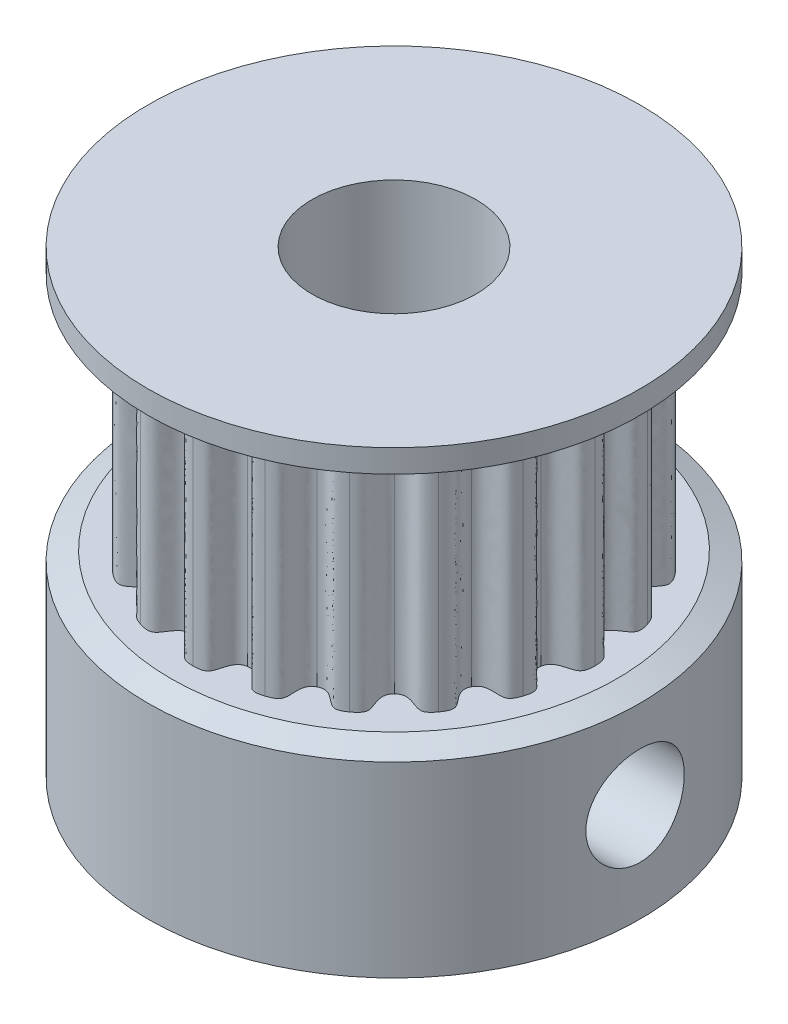
SolidWorks part; units mm, degrees
material "6063-T5"
ref_plane "Front Plane" through (0, 0, 0) normal (0, 0, 1) x (1, 0, 0)
ref_plane "Top Plane" through (0, 0, 0) normal (0, 1, 0) x (1, 0, 0)
ref_plane "Right Plane" through (0, 0, 0) normal (1, 0, 0) x (0, 0, -1)
sketch "Sketch1" plane through (0, 0, 0) normal (0, 1, 0) x (1, 0, 0)
  circle A0 centre (0, 0) radius 7.5
  dimension "D1" = 15
extrude "Boss-Extrude1" add sketch "Sketch1" along normal blind 6 contours A0
sketch "Sketch2" plane through (0, 6, 0) normal (0, 1, 0) x (1, 0, 0)
  line L0 (0, 6.1275) -> (0, 5.3775) construction
  line L1 (1.8935, 5.8276) -> (1.6617, 5.1143) construction
  line L2 (0.9585, 6.052) -> (0.8412, 5.3113) construction
  circle A0 centre (0, 0) radius 6.1275
  circle A1 centre (0, 0) radius 5.3775 construction
  spline S0 degree 3 poles (0, 6.1275) (0.3458, 6.1275) (0.4361, 5.9343) (0.5475, 5.3578) (0.8412, 5.3113) knots 0 0 0 0 0.372907 1 1 1 1
  spline S1 degree 3 poles (1.8935, 5.8276) (1.5646, 5.9344) (1.419, 5.7786) (1.135, 5.2647) (0.8412, 5.3113) knots 0 0 0 0 0.372907 1 1 1 1
  spline S2 degree 3 poles (3.6016, 4.9572) (3.3681, 5.1259) (3.0728, 5.1167) (2.729, 4.6418) (2.4347, 4.7947) knots 0 0 0 0 0.382401 1 1 1 1
  spline S3 degree 3 poles (1.8935, 5.8276) (2.162, 5.7403) (2.3095, 5.4903) (2.1415, 4.9436) (2.4347, 4.7947) knots 0 0 0 0 0.37474 1 1 1 1
  spline S4 degree 3 poles (4.9572, 3.6016) (4.7873, 3.8342) (4.5035, 3.9167) (4.0298, 3.5713) (3.7972, 3.8077) knots 0 0 0 0 0.382401 1 1 1 1
  spline S5 degree 3 poles (3.6016, 4.9572) (3.83, 4.7913) (3.8931, 4.5079) (3.5643, 4.0399) (3.7972, 3.8077) knots 0 0 0 0 0.37474 1 1 1 1
  spline S6 degree 3 poles (5.8276, 1.8935) (5.7378, 2.1672) (5.4934, 2.3334) (4.9362, 2.1512) (4.788, 2.4479) knots 0 0 0 0 0.382401 1 1 1 1
  spline S7 degree 3 poles (4.9572, 3.6016) (5.1231, 3.3733) (5.0955, 3.0843) (4.6383, 2.7408) (4.788, 2.4479) knots 0 0 0 0 0.37474 1 1 1 1
  spline S8 degree 3 poles (6.1275, 0) (6.1267, 0.288) (5.9456, 0.5216) (5.3594, 0.5206) (5.3101, 0.8485) knots 0 0 0 0 0.382401 1 1 1 1
  spline S9 degree 3 poles (5.8276, 1.8935) (5.9148, 1.625) (5.7992, 1.3587) (5.2582, 1.1733) (5.3101, 0.8485) knots 0 0 0 0 0.37474 1 1 1 1
  spline S10 degree 3 poles (5.8276, -1.8935) (5.9158, -1.6193) (5.8158, -1.3412) (5.2579, -1.1611) (5.3124, -0.8339) knots 0 0 0 0 0.382401 1 1 1 1
  spline S11 degree 3 poles (6.1275, 0) (6.1275, -0.2823) (5.9353, -0.4999) (5.3634, -0.509) (5.3124, -0.8339) knots 0 0 0 0 0.37474 1 1 1 1
  spline S12 degree 3 poles (4.9572, -3.6016) (5.1259, -3.3681) (5.1167, -3.0728) (4.6418, -2.729) (4.7947, -2.4347) knots 0 0 0 0 0.382401 1 1 1 1
  spline S13 degree 3 poles (5.8276, -1.8935) (5.7403, -2.162) (5.4903, -2.3095) (4.9436, -2.1415) (4.7947, -2.4347) knots 0 0 0 0 0.37474 1 1 1 1
  spline S14 degree 3 poles (3.6016, -4.9572) (3.8342, -4.7873) (3.9167, -4.5035) (3.5713, -4.0298) (3.8077, -3.7972) knots 0 0 0 0 0.382401 1 1 1 1
  spline S15 degree 3 poles (4.9572, -3.6016) (4.7913, -3.83) (4.5079, -3.8931) (4.0399, -3.5643) (3.8077, -3.7972) knots 0 0 0 0 0.37474 1 1 1 1
  spline S16 degree 3 poles (1.8935, -5.8276) (2.1672, -5.7378) (2.3334, -5.4934) (2.1512, -4.9362) (2.4479, -4.788) knots 0 0 0 0 0.382401 1 1 1 1
  spline S17 degree 3 poles (3.6016, -4.9572) (3.3733, -5.1231) (3.0843, -5.0955) (2.7408, -4.6383) (2.4479, -4.788) knots 0 0 0 0 0.37474 1 1 1 1
  spline S18 degree 3 poles (0, -6.1275) (0.288, -6.1267) (0.5216, -5.9456) (0.5206, -5.3594) (0.8485, -5.3101) knots 0 0 0 0 0.382401 1 1 1 1
  spline S19 degree 3 poles (1.8935, -5.8276) (1.625, -5.9148) (1.3587, -5.7992) (1.1733, -5.2582) (0.8485, -5.3101) knots 0 0 0 0 0.37474 1 1 1 1
  spline S20 degree 3 poles (-1.8935, -5.8276) (-1.6193, -5.9158) (-1.3412, -5.8158) (-1.1611, -5.2579) (-0.8339, -5.3124) knots 0 0 0 0 0.382401 1 1 1 1
  spline S21 degree 3 poles (0, -6.1275) (-0.2823, -6.1275) (-0.4999, -5.9353) (-0.509, -5.3634) (-0.8339, -5.3124) knots 0 0 0 0 0.37474 1 1 1 1
  spline S22 degree 3 poles (-3.6016, -4.9572) (-3.3681, -5.1259) (-3.0728, -5.1167) (-2.729, -4.6418) (-2.4347, -4.7947) knots 0 0 0 0 0.382401 1 1 1 1
  spline S23 degree 3 poles (-1.8935, -5.8276) (-2.162, -5.7403) (-2.3095, -5.4903) (-2.1415, -4.9436) (-2.4347, -4.7947) knots 0 0 0 0 0.37474 1 1 1 1
  spline S24 degree 3 poles (-4.9572, -3.6016) (-4.7873, -3.8342) (-4.5035, -3.9167) (-4.0298, -3.5713) (-3.7972, -3.8077) knots 0 0 0 0 0.382401 1 1 1 1
  spline S25 degree 3 poles (-3.6016, -4.9572) (-3.83, -4.7913) (-3.8931, -4.5079) (-3.5643, -4.0399) (-3.7972, -3.8077) knots 0 0 0 0 0.37474 1 1 1 1
  spline S26 degree 3 poles (-5.8276, -1.8935) (-5.7378, -2.1672) (-5.4934, -2.3334) (-4.9362, -2.1512) (-4.788, -2.4479) knots 0 0 0 0 0.382401 1 1 1 1
  spline S27 degree 3 poles (-4.9572, -3.6016) (-5.1231, -3.3733) (-5.0955, -3.0843) (-4.6383, -2.7408) (-4.788, -2.4479) knots 0 0 0 0 0.37474 1 1 1 1
  spline S28 degree 3 poles (-6.1275, 0) (-6.1267, -0.288) (-5.9456, -0.5216) (-5.3594, -0.5206) (-5.3101, -0.8485) knots 0 0 0 0 0.382401 1 1 1 1
  spline S29 degree 3 poles (-5.8276, -1.8935) (-5.9148, -1.625) (-5.7992, -1.3587) (-5.2582, -1.1733) (-5.3101, -0.8485) knots 0 0 0 0 0.37474 1 1 1 1
  spline S30 degree 3 poles (-5.8276, 1.8935) (-5.9158, 1.6193) (-5.8158, 1.3412) (-5.2579, 1.1611) (-5.3124, 0.8339) knots 0 0 0 0 0.382401 1 1 1 1
  spline S31 degree 3 poles (-6.1275, 0) (-6.1275, 0.2823) (-5.9353, 0.4999) (-5.3634, 0.509) (-5.3124, 0.8339) knots 0 0 0 0 0.37474 1 1 1 1
  spline S32 degree 3 poles (-4.9572, 3.6016) (-5.1259, 3.3681) (-5.1167, 3.0728) (-4.6418, 2.729) (-4.7947, 2.4347) knots 0 0 0 0 0.382401 1 1 1 1
  spline S33 degree 3 poles (-5.8276, 1.8935) (-5.7403, 2.162) (-5.4903, 2.3095) (-4.9436, 2.1415) (-4.7947, 2.4347) knots 0 0 0 0 0.37474 1 1 1 1
  spline S34 degree 3 poles (-3.6016, 4.9572) (-3.8342, 4.7873) (-3.9167, 4.5035) (-3.5713, 4.0298) (-3.8077, 3.7972) knots 0 0 0 0 0.382401 1 1 1 1
  spline S35 degree 3 poles (-4.9572, 3.6016) (-4.7913, 3.83) (-4.5079, 3.8931) (-4.0399, 3.5643) (-3.8077, 3.7972) knots 0 0 0 0 0.37474 1 1 1 1
  spline S36 degree 3 poles (-1.8935, 5.8276) (-2.1672, 5.7378) (-2.3334, 5.4934) (-2.1512, 4.9362) (-2.4479, 4.788) knots 0 0 0 0 0.382401 1 1 1 1
  spline S37 degree 3 poles (-3.6016, 4.9572) (-3.3733, 5.1231) (-3.0843, 5.0955) (-2.7408, 4.6383) (-2.4479, 4.788) knots 0 0 0 0 0.37474 1 1 1 1
  spline S38 degree 3 poles (0, 6.1275) (-0.288, 6.1267) (-0.5216, 5.9456) (-0.5206, 5.3594) (-0.8485, 5.3101) knots 0 0 0 0 0.382401 1 1 1 1
  spline S39 degree 3 poles (-1.8935, 5.8276) (-1.625, 5.9148) (-1.3587, 5.7992) (-1.1733, 5.2582) (-0.8485, 5.3101) knots 0 0 0 0 0.37474 1 1 1 1
  point P10 (0, 0)
  point P14 (0, 0)
  point P153 (0, 0)
  dimension "D1" = 12.2549
  dimension "D2" = 0.75
  dimension "D3" = 2
  dimension "D4" = 2
extrude "Boss-Extrude2" add sketch "Sketch2" along normal blind 7 contours S39 S36 S37 S34 S35 S32 S33 S30 S31 S28 S29 S26 S27 S24 S25 S22 S23 S20 S21 S18 S19 S16 S17 S14 S15 S12 S13 S10 S11 S8 S9 S6 S7 S4 S5 S2 S3 S1 S0 S38
sketch "Sketch3" plane through (0, 13, 0) normal (0, 1, 0) x (1, 0, 0)
  circle A0 centre (0, 0) radius 7.5 construction
  circle A1 centre (0, 0) radius 7.5
extrude "Boss-Extrude3" add sketch "Sketch3" along normal blind 1
chamfer "Chamfer1" distance 0.7 distance2 0.3 1 edges at (0, 13, 7.5)
chamfer "Chamfer2" distance 0.3 distance2 0.7 1 edges at (0, 6, 7.5)
sketch "Sketch4" plane through (0, 0, 0) normal (0, -1, 0) x (1, 0, 0)
  circle A0 centre (0, 0) radius 2.5
  dimension "D1" = 5
extrude "Cut-Extrude1" cut sketch "Sketch4" against normal through all
sketch "Sketch5" plane through (0, 0, 0) normal (1, 0, 0) x (0, 0, -1)
  circle A0 centre (0, 3) radius 1.5
  dimension "D1" = 3
  dimension "D2" = 3
extrude "Cut-Extrude2" cut sketch "Sketch5" along normal through all
sketch "Sketch6" plane through (0, 0, 0) normal (0, 0, 1) x (1, 0, 0)
  circle A0 centre (0, 3) radius 1.5
  dimension "D1" = 3
  dimension "D2" = 3
extrude "Cut-Extrude3" cut sketch "Sketch6" against normal through all
ref_plane "Plane1" through (0, 9.5, 0) normal (0, 1, 0) x (1, 0, 0)
sketch "Sketch7" plane through (0, 6, 0) normal (0, 1, 0) x (1, 0, 0)
  circle A0 centre (0, 0) radius 6.1275 construction
sketch "Sketch8" plane through (0, 9.5, 0) normal (0, 1, 0) x (1, 0, 0)
  circle A0 centre (0, 0) radius 6.1275 construction
  circle A1 centre (0, 0) radius 6.1275
